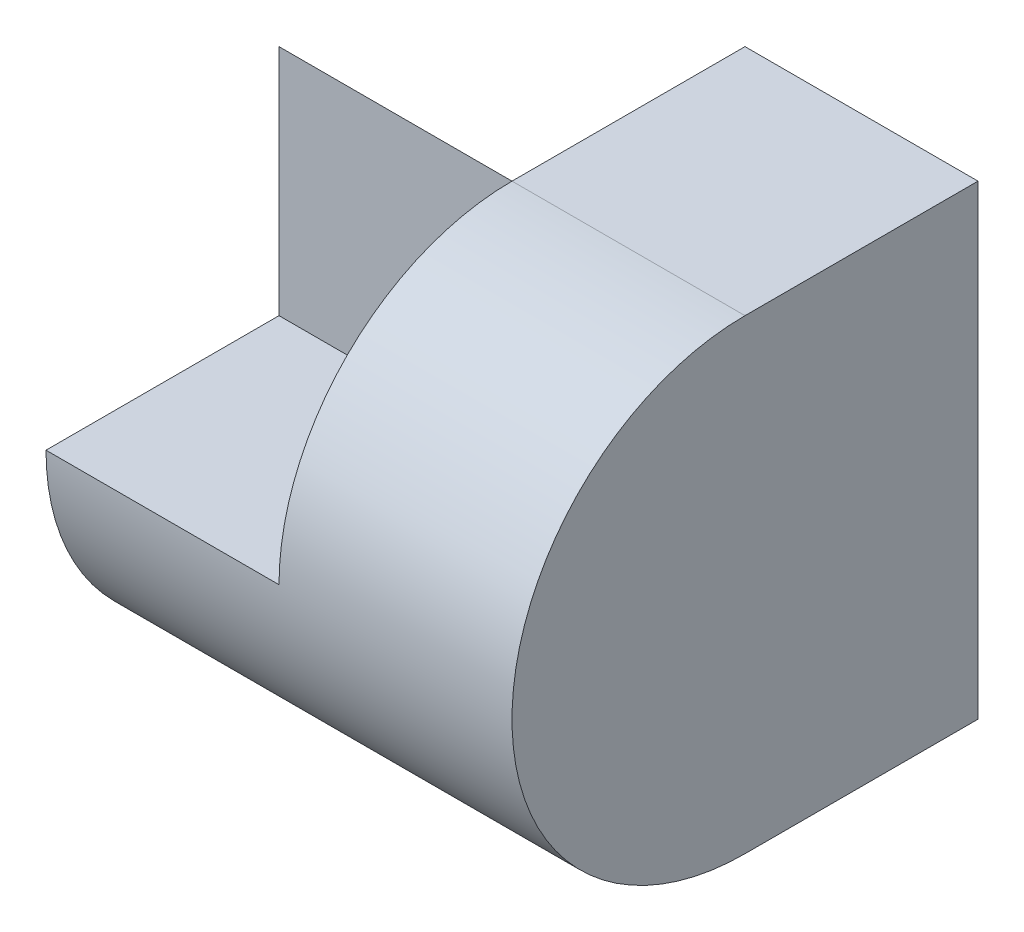
SolidWorks part; units mm, degrees
ref_plane "Front" through (0, 0, 0) normal (0, 0, 1) x (1, 0, 0)
ref_plane "Top" through (0, 0, 0) normal (0, 1, 0) x (1, 0, 0)
ref_plane "Right" through (0, 0, 0) normal (1, 0, 0) x (0, 0, -1)
sketch "Sketch1" plane through (0, 0, 0) normal (0, 1, 0) x (1, 0, 0)
  line L1 (-2, -2) -> (2, -2)
  line L2 (-2, -2) -> (-2, 2)
  line L3 (-2, 2) -> (2, 2)
  line L4 (2, -2) -> (2, 2)
  line L5 (-2, -2) -> (2, 2) construction
  line L6 (-2, 2) -> (2, -2) construction
  point P0 (0, 0)
  dimension "D1" = 4
  dimension "D2" = 4
extrude "Boss-Extrude1" add sketch "Sketch1" along normal blind 4
sketch "Sketch2" plane through (-2, 0, 0) normal (-1, 0, 0) x (0, 0, 1)
  line L0 (-2, 2) -> (0, 4)
  line L3 (0, 4) -> (0, 2)
  line L5 (0, 2) -> (2, 2)
  line L9 (-2, 0) -> (2, 0)
  line L10 (2, 0) -> (2, 4)
  line L11 (2, 4) -> (-2, 4)
  line L12 (-2, 4) -> (-2, 0)
  line L13 (-2, 0) -> (2, 0)
  line L14 (2, 0) -> (2, 4)
  line L15 (2, 4) -> (-2, 4)
  line L16 (-2, 4) -> (-2, 0)
  dimension "D1" = 0
extrude "Cut-Extrude1" cut sketch "Sketch2" against normal blind 2
sketch "Sketch3" plane through (0, 0, 0) normal (-1, 0, 0) x (0, 0, 1)
  line L0 (2, 2) -> (0, 2) construction
  line L1 (0, 2) -> (0, 4) construction
  line L2 (0, 4) -> (-2, 2) construction
  line L3 (-2, 2) -> (-2, 0) construction
  line L4 (-2, 0) -> (2, 0) construction
  line L5 (2, 0) -> (2, 2) construction
  line L6 (0, 4) -> (0, 2) construction
  line L7 (0, 2) -> (2, 2) construction
  line L8 (2, 2) -> (2, 4) construction
  line L9 (2, 4) -> (0, 4) construction
  line L10 (2, 2) -> (0, 2)
  line L11 (0, 2) -> (0, 4)
  line L12 (0, 4) -> (-2, 2)
  line L13 (-2, 2) -> (-2, 0)
  line L14 (-2, 0) -> (2, 0)
  line L15 (2, 0) -> (2, 2)
  line L16 (0, 4) -> (0, 2)
  line L17 (0, 2) -> (2, 2)
  line L18 (2, 2) -> (2, 4)
  line L19 (2, 4) -> (0, 4)
  arc A0 (0, 4) -> (0, 0) centre (0, 2) cw
  line M3 (2, 2) -> (2, 4)
  line M4 (2, 4) -> (0, 4)
extrude "Cut-Extrude2" cut sketch "Sketch3" against normal mid plane 10 contours A0 M4 M3 | L15 A0 L14
